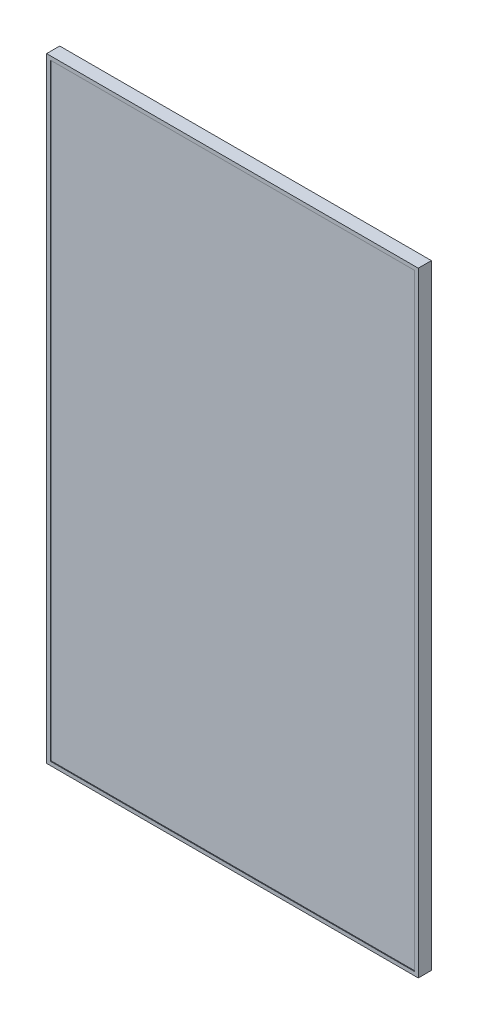
SolidWorks part; units mm, degrees
material "Aleación 6061"
ref_plane "Alzado" through (0, 0, 0) normal (0, 0, 1) x (1, 0, 0)
ref_plane "Planta" through (0, 0, 0) normal (0, 1, 0) x (1, 0, 0)
ref_plane "Vista lateral" through (0, 0, 0) normal (1, 0, 0) x (0, 0, -1)
sketch "Croquis1" plane through (0, 0, 0) normal (0, 0, 1) x (1, 0, 0)
  line L1 (-495.5, -819.5) -> (495.5, -819.5)
  line L2 (-495.5, -819.5) -> (-495.5, 819.5)
  line L3 (-495.5, 819.5) -> (495.5, 819.5)
  line L4 (495.5, -819.5) -> (495.5, 819.5)
  line L5 (-495.5, -819.5) -> (495.5, 819.5) construction
  line L6 (-495.5, 819.5) -> (495.5, -819.5) construction
  point P0 (0, 0)
  dimension "D1" = 991
  dimension "D2" = 1639
extrude "Saliente-Extruir1" add sketch "Croquis1" along normal blind 5
sketch "Croquis2" plane through (0, 0, 5) normal (0, 0, 1) x (1, 0, 0)
  line L0 (495.5, 819.5) -> (-495.5, 819.5) construction
  line L1 (-485.5, -809.5) -> (485.5, -809.5)
  line L2 (-485.5, -809.5) -> (-485.5, 809.5)
  line L3 (-485.5, 809.5) -> (485.5, 809.5)
  line L4 (485.5, -809.5) -> (485.5, 809.5)
  line L5 (-485.5, -809.5) -> (485.5, 809.5) construction
  line L6 (-485.5, 809.5) -> (485.5, -809.5) construction
  line L7 (495.5, -819.5) -> (495.5, 819.5) construction
  point P0 (0, 0)
  dimension "D1" = 10
  dimension "D2" = 10
extrude "Cortar-Extruir1" cut sketch "Croquis2" against normal blind 2
sketch "Croquis3" plane through (0, 0, 0) normal (0, 0, -1) x (-1, 0, 0)
  line L0 (-495.5, 819.5) -> (495.5, 819.5) construction
  line L1 (-494.5, -818.5) -> (494.5, -818.5)
  line L2 (-494.5, -818.5) -> (-494.5, 818.5)
  line L3 (-494.5, 818.5) -> (494.5, 818.5)
  line L4 (494.5, -818.5) -> (494.5, 818.5)
  line L5 (-494.5, -818.5) -> (494.5, 818.5) construction
  line L6 (-494.5, 818.5) -> (494.5, -818.5) construction
  line L7 (495.5, 819.5) -> (495.5, -819.5) construction
  line L8 (495.5, -819.5) -> (-495.5, -819.5) construction
  line L9 (-495.5, -819.5) -> (-495.5, 819.5) construction
  line L10 (495.5, -819.5) -> (-495.5, -819.5)
  line L11 (-495.5, -819.5) -> (-495.5, 819.5)
  line L12 (495.5, 819.5) -> (495.5, -819.5)
  line L13 (-495.5, 819.5) -> (495.5, 819.5)
  point P0 (0, 0)
  dimension "D1" = 1
  dimension "D2" = 1
extrude "Saliente-Extruir2" add sketch "Croquis3" along normal blind 30
sketch "Croquis4" plane through (0, 0, -30) normal (0, 0, -1) x (-1, 0, 0)
  line L0 (495.5, 819.5) -> (-495.5, 819.5) construction
  line L1 (-460.5, -784.5) -> (460.5, -784.5)
  line L2 (-460.5, -784.5) -> (-460.5, 784.5)
  line L3 (-460.5, 784.5) -> (460.5, 784.5)
  line L4 (460.5, -784.5) -> (460.5, 784.5)
  line L5 (-460.5, -784.5) -> (460.5, 784.5) construction
  line L6 (-460.5, 784.5) -> (460.5, -784.5) construction
  line L7 (495.5, -819.5) -> (495.5, 819.5) construction
  line L8 (-495.5, -819.5) -> (495.5, -819.5) construction
  line L9 (-495.5, 819.5) -> (-495.5, -819.5) construction
  line L10 (-495.5, -819.5) -> (495.5, -819.5)
  line L11 (-495.5, 819.5) -> (-495.5, -819.5)
  line L12 (495.5, -819.5) -> (495.5, 819.5)
  line L13 (495.5, 819.5) -> (-495.5, 819.5)
  point P0 (0, 0)
  dimension "D1" = 35
  dimension "D2" = 35
extrude "Saliente-Extruir3" add sketch "Croquis4" against normal blind 1
sketch "Croquis5" plane through (0, 0, -30) normal (0, 0, -1) x (-1, 0, 0)
  line L0 (-478, 652.5) -> (-478, 648.5) construction
  line L1 (-473, 652.5) -> (-473, 648.5)
  line L2 (-483, 652.5) -> (-483, 648.5)
  line L3 (-495.5, 525.5) -> (-460.5, 525.5) construction
  line L4 (-460.5, 784.5) -> (-460.5, -784.5) construction
  line L5 (495.5, 819.5) -> (-495.5, 819.5) construction
  line L6 (-495.5, 819.5) -> (-495.5, -819.5) construction
  line L7 (-478, 398.5) -> (-478, 402.5) construction
  line L8 (-473, 398.5) -> (-473, 402.5)
  line L9 (-483, 398.5) -> (-483, 402.5)
  line L10 (-20.8844, 0) -> (28.4628, 0) construction
  line L11 (0, 29.7856) -> (0, -22.0289) construction
  line L12 (-478, -652.5) -> (-478, -648.5) construction
  line L13 (-473, -652.5) -> (-473, -648.5)
  line L14 (-483, -652.5) -> (-483, -648.5)
  line L15 (-478, -398.5) -> (-478, -402.5) construction
  line L16 (-473, -398.5) -> (-473, -402.5)
  line L17 (-483, -398.5) -> (-483, -402.5)
  line L18 (478, -652.5) -> (478, -648.5) construction
  line L19 (473, -652.5) -> (473, -648.5)
  line L20 (483, -652.5) -> (483, -648.5)
  line L21 (478, -398.5) -> (478, -402.5) construction
  line L22 (473, -398.5) -> (473, -402.5)
  line L23 (483, -398.5) -> (483, -402.5)
  line L24 (478, 398.5) -> (478, 402.5) construction
  line L25 (473, 398.5) -> (473, 402.5)
  line L26 (483, 398.5) -> (483, 402.5)
  line L27 (478, 652.5) -> (478, 648.5) construction
  line L28 (473, 652.5) -> (473, 648.5)
  line L29 (483, 652.5) -> (483, 648.5)
  arc A0 (-473, 652.5) -> (-483, 652.5) centre (-478, 652.5) ccw
  arc A1 (-483, 648.5) -> (-473, 648.5) centre (-478, 648.5) ccw
  arc A2 (-473, 398.5) -> (-483, 398.5) centre (-478, 398.5) cw
  arc A3 (-483, 402.5) -> (-473, 402.5) centre (-478, 402.5) cw
  circle A4 centre (-478, 0) radius 2.5
  arc A5 (-473, -652.5) -> (-483, -652.5) centre (-478, -652.5) cw
  arc A6 (-483, -648.5) -> (-473, -648.5) centre (-478, -648.5) cw
  arc A7 (-473, -398.5) -> (-483, -398.5) centre (-478, -398.5) ccw
  arc A8 (-483, -402.5) -> (-473, -402.5) centre (-478, -402.5) ccw
  arc A9 (473, -652.5) -> (483, -652.5) centre (478, -652.5) ccw
  arc A10 (483, -648.5) -> (473, -648.5) centre (478, -648.5) ccw
  arc A11 (473, -398.5) -> (483, -398.5) centre (478, -398.5) cw
  arc A12 (483, -402.5) -> (473, -402.5) centre (478, -402.5) cw
  arc A13 (473, 398.5) -> (483, 398.5) centre (478, 398.5) ccw
  arc A14 (483, 402.5) -> (473, 402.5) centre (478, 402.5) ccw
  arc A15 (473, 652.5) -> (483, 652.5) centre (478, 652.5) cw
  arc A16 (483, 648.5) -> (473, 648.5) centre (478, 648.5) cw
  circle A17 centre (478, 0) radius 2.5
  point P2 (-478, 650.5)
  point P17 (-478, 400.5)
  point P26 (-460.5, 0)
  point P31 (28.4628, 0)
  point P34 (-478, -650.5)
  point P41 (-478, -400.5)
  point P48 (478, -650.5)
  point P55 (478, -400.5)
  point P62 (478, 400.5)
  point P69 (478, 650.5)
  dimension "D4" = 5
  dimension "D6" = 5
  dimension "D1" = 167
  dimension "D2" = 17.5
  dimension "D3" = 171
  dimension "D5" = 294
  dimension "D7" = 17.5
extrude "Cortar-Extruir2" cut sketch "Croquis5" against normal blind 1
